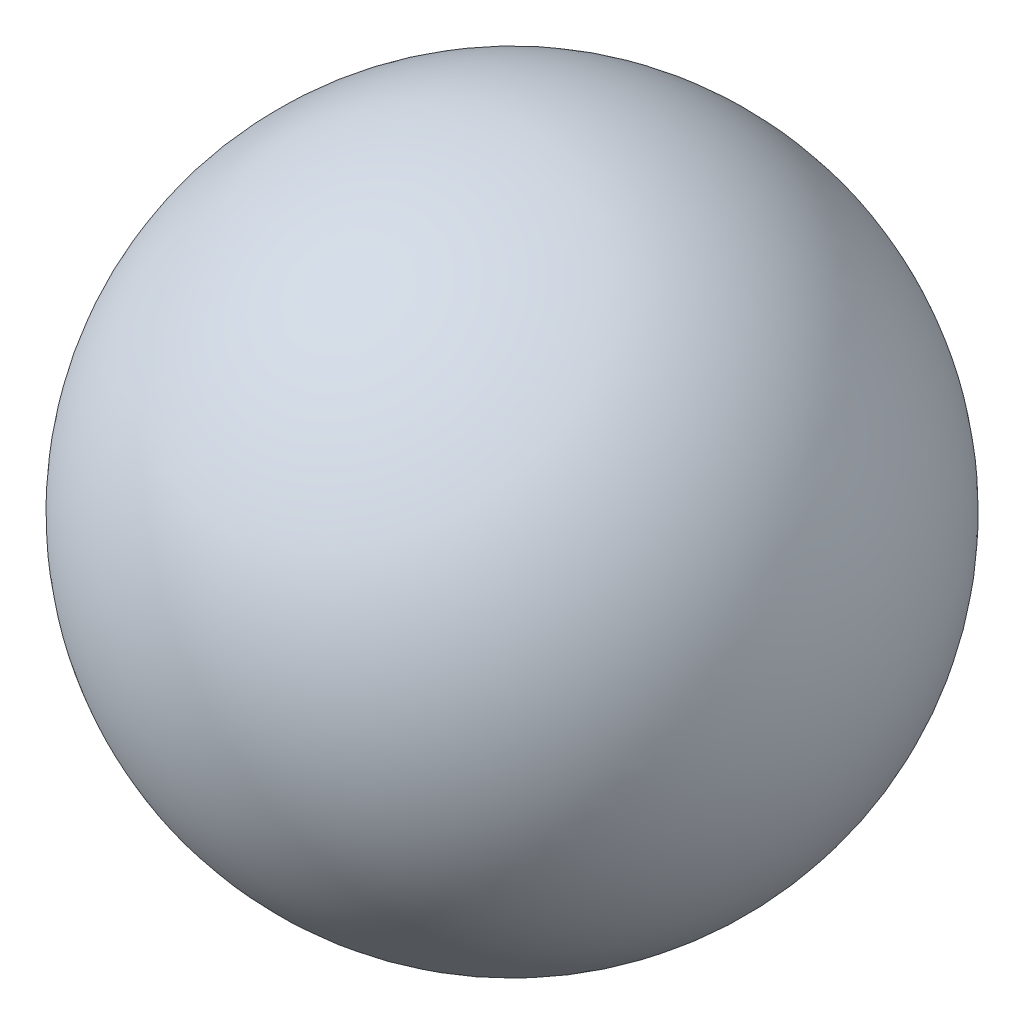
SolidWorks part; units mm, degrees
material "Chrome Stainless Steel"
ref_plane "Front Plane" through (0, 0, 0) normal (0, 0, 1) x (1, 0, 0)
ref_plane "Top Plane" through (0, 0, 0) normal (0, 1, 0) x (1, 0, 0)
ref_plane "Right Plane" through (0, 0, 0) normal (1, 0, 0) x (0, 0, -1)
sketch "Sketch1" plane through (0, 0, 0) normal (0, 1, 0) x (1, 0, 0)
  line L0 (0, 0) -> (0, 19.05)
  arc A0 (0, 0) -> (0, 19.05) centre (0, 9.525) cw
  dimension "D1" = 19.05
revolve "Revolve1" add sketch "Sketch1" angle 360 about L0
sketch "Sketch2" plane through (0, 0, 0) normal (0, 1, 0) x (1, 0, 0)
  line L0 (0, 0) -> (0, 19.05) construction
  circle A0 centre (0, 9.525) radius 9.525 construction
  circle A1 centre (0, 9.525) radius 9.525 construction
  point P8 (0, 9.525)
